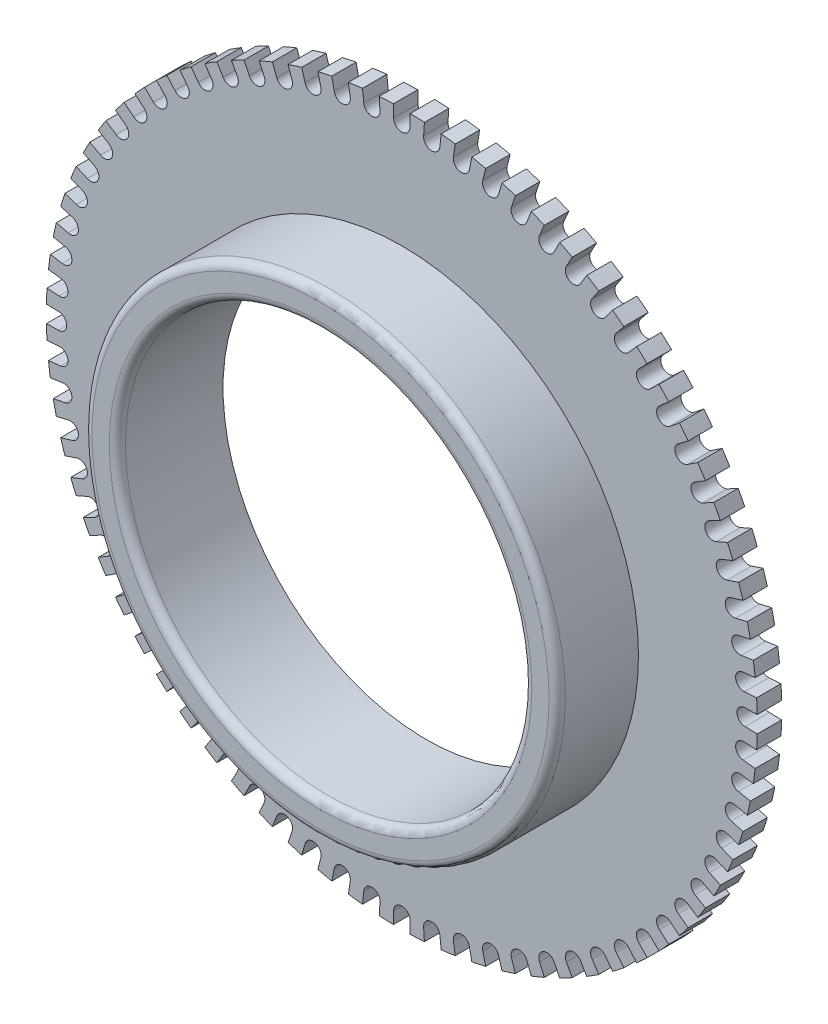
SolidWorks part; units mm, degrees
ref_plane "Front Plane" through (0, 0, 0) normal (0, 0, 1) x (1, 0, 0)
ref_plane "Top Plane" through (0, 0, 0) normal (0, 1, 0) x (1, 0, 0)
ref_plane "Right Plane" through (0, 0, 0) normal (1, 0, 0) x (0, 0, -1)
sketch "Sketch1" plane through (0, 0, 0) normal (0, 0, 1) x (1, 0, 0)
  circle A0 centre (0, 0) radius 63.5
  circle A1 centre (0, 0) radius 111.125
  dimension "D1" = 222.25
  dimension "D2" = 127
extrude "Boss-Extrude1" add sketch "Sketch1" along normal blind 7.62
sketch "Sketch2" plane through (0, 0, 7.62) normal (0, 0, 1) x (1, 0, 0)
  line L0 (0, 0) -> (0, 107.2918) construction
  line L1 (-2.54, 107.2918) -> (-2.6638, 112.5206)
  line L2 (2.54, 107.2918) -> (2.6638, 112.5206)
  line L3 (2.6638, 112.5206) -> (-2.6638, 112.5206)
  line L4 (0, 111.125) -> (0, 120.5858) construction
  arc A0 (2.5398, 107.2617) -> (-2.5398, 107.2617) centre (0, 0) ccw
  arc A1 (-2.54, 107.2918) -> (2.54, 107.2918) centre (0, 107.2918) ccw
  point P3 (0, 107.2617)
  dimension "D1" = 2.54
extrude "Cut-Extrude1" cut sketch "Sketch2" against normal through all contours L3 L1 A1 L2
pattern_circular "CirPattern1" count 72 over 360 about axis through (0, 0, 0) along (0, 0, 1) of "Cut-Extrude1"
sketch "Sketch3" plane through (0, 0, 7.62) normal (0, 0, 1) x (1, 0, 0)
  circle A0 centre (0, 0) radius 63.5
  circle A1 centre (0, 0) radius 73.9694
extrude "Boss-Extrude2" add sketch "Sketch3" along normal blind 25.4
fillet "Fillet1" radius 2.54 2 edges at (63.5, 0, 33.02) (73.9694, 0, 33.02)
sketch "Sketch4" plane through (0, 0, 33.02) normal (0, 0, 1) x (1, 0, 0)
  line L1 (-5.3826, -59.116) -> (10.8131, -59.116)
  line L2 (-5.3826, -59.116) -> (-5.3826, -73.1748)
  line L3 (-5.3826, -73.1748) -> (10.8131, -73.1748)
  line L4 (10.8131, -59.116) -> (10.8131, -73.1748)
  circle A0 centre (0, 0) radius 73.9694 construction
